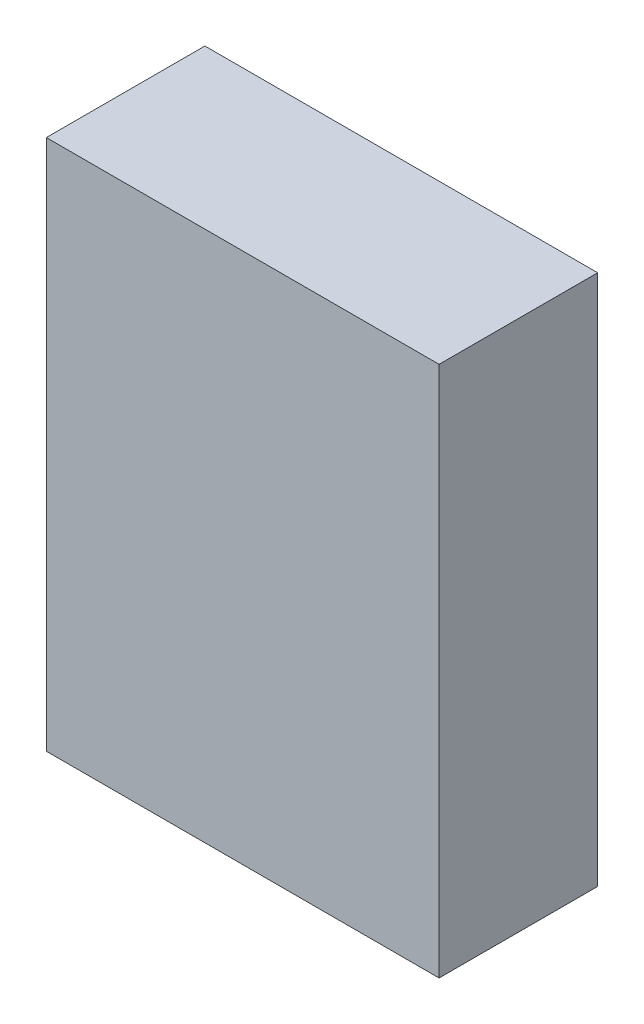
SolidWorks part; units mm, degrees
ref_plane "Front Plane" through (0, 0, 0) normal (0, 0, 1) x (1, 0, 0)
ref_plane "Top Plane" through (0, 0, 0) normal (0, 1, 0) x (1, 0, 0)
ref_plane "Right Plane" through (0, 0, 0) normal (1, 0, 0) x (0, 0, -1)
sketch "Sketch1" plane through (0, 0, 0) normal (0, 0, 1) x (1, 0, 0)
  line L0 (0, 0) -> (33.8319, 0) construction
  line L1 (37.6419, -43.18) -> (190.0419, -43.18) construction
  line L2 (-29.99, 35.7) -> (-29.99, -35.7) construction
  line L3 (33.8319, 43.18) -> (33.8319, -43.18)
  line L4 (33.8319, -43.18) -> (-29.99, -43.18)
  line L5 (-29.99, 0) -> (-29.99, -43.18)
  line L7 (37.6419, 43.18) -> (37.6419, -43.18) construction
  line L8 (-29.99, 0) -> (-29.99, 43.18)
  line L9 (33.8319, 43.18) -> (-29.99, 43.18)
  dimension "D1" = 3.81
extrude "Boss-Extrude1" add sketch "Sketch1" along normal offset from surface (25.769 mm away) 2.54
